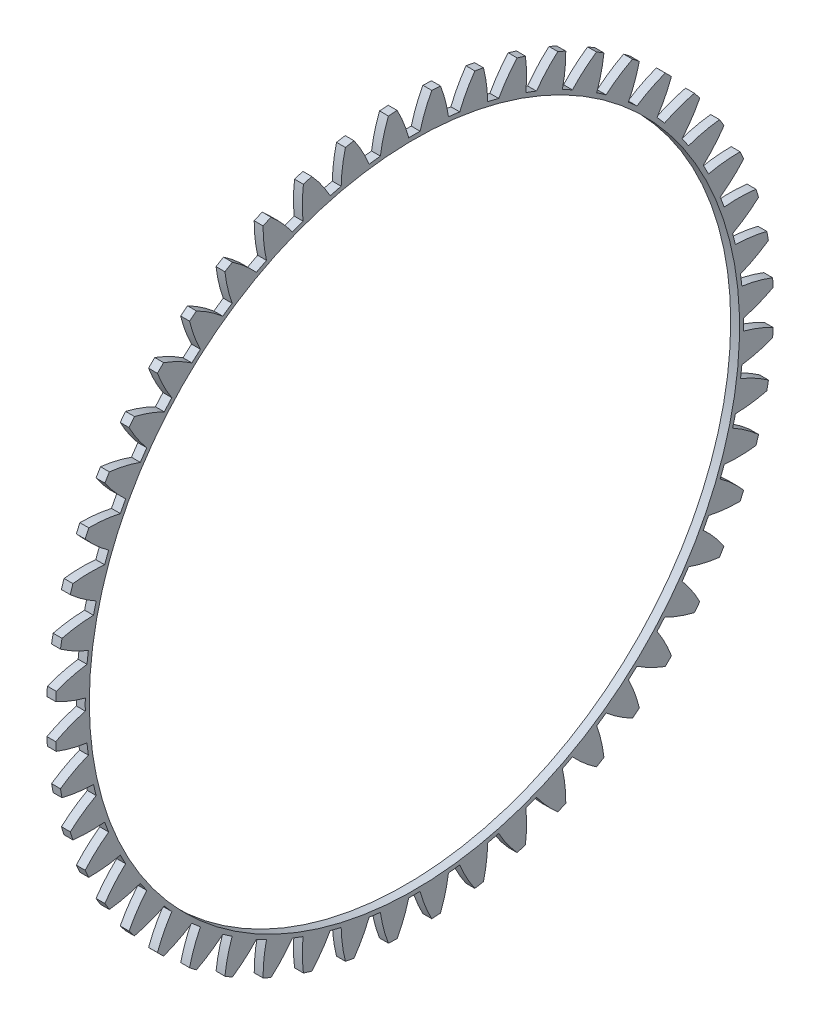
SolidWorks part; units mm, degrees
ref_plane "Plane1" through (0, 0, 0) normal (0, 0, 1) x (1, 0, 0)
ref_plane "Plane2" through (0, 0, 0) normal (0, 1, 0) x (1, 0, 0)
ref_plane "Plane3" through (0, 0, 0) normal (1, 0, 0) x (0, 0, -1)
sketch "HoldingSke" plane through (0, 0, 0) normal (0, 1, 0) x (1, 0, 0)
  line L0 (0, 0) -> (0.1368, -0.1751)
  line L1 (-15, 0) -> (100, 0) construction
  line L2 (0, 0) -> (-2.1039, 2.3779)
  line L3 (0, 0) -> (-11.863, 4.5341)
  line L4 (0, 0) -> (5.3169, 6.8053)
  line L5 (0, 0) -> (-46.8476, -17.4728)
  line L6 (0, 0) -> (-2.4869, -1.6779)
  line L7 (-2.1039, 2.3779) -> (8.6586, 51.2059)
  line L8 (-76.2, 54.61) -> (-64.8, 54.61)
  line L9 (-71.009, 38.7566) -> (-53.1078, 45.2721)
  line L10 (-76.2, 71.12) -> (104.1128, 71.12)
  line L11 (0, 0) -> (-3, 0)
  line L12 (-76.2, 101.6) -> (-76.053, 101.6)
  line L13 (24.9733, 27.94) -> (52.9518, 28.4284)
  line L14 (24.9733, 27.94) -> (24.9743, 27.94)
  line L15 (24.9733, 27.94) -> (100.4006, 29.5858)
  line L16 (-63.627, -4.5) -> (-12.827, -4.5)
  circle A0 centre (0, 0) radius 110
  circle A1 centre (0, 0) radius 37.5
  circle A2 centre (0, 0) radius 37.5
  circle A3 centre (0, 0) radius 110
  dimension "MHD" = 75
  dimension "Hub_dia" = 75
  dimension "Bore" = 220
  dimension "MBD" = 220
  dimension "Num_teeth" = 52
  dimension "Pitch" = 0.2222
  dimension "Overall_len" = 50
  dimension "Show_teeth" = 52
  dimension "Thickness" = 3
  dimension "OAL" = 50.0001
  dimension "T_dim" = 11.4
  dimension "Ap" = 20
  dimension "H" = 19.05
  dimension "Pitch_radius" = 180.3128
  dimension "Width" = 3
  dimension "Backlash" = 0.147
  dimension "Addendum_fac" = 1
  dimension "Dedendum_fac" = 1.25
  dimension "Clearance_fac" = 0.25
  dimension "Dedendum_add" = 0.001
  dimension "Module" = 4.5
sketch "BasProSke" plane through (0, 0, 0) normal (0, 1, 0) x (1, 0, 0)
  line L0 (-10, 0) -> (60, 0) construction
  line L1 (0, 0) -> (0, 121.5)
  line L2 (0, 0) -> (3, 0)
  line L3 (3, 0) -> (3, 121.5)
  line L4 (3, 121.5) -> (0, 121.5)
  dimension "Thickness" = 3
  dimension "Diameter" = 243
revolve "Base-Revolve" add sketch "BasProSke" angle 360 about L0
sketch "TooCutSke" plane through (0, 0, 0) normal (1, 0, 0) x (0, 0, -1)
  line L1 (0, 0) -> (0, 107) construction
  line L2 (0, 0) -> (-3.791, 116.9386) construction
  line L3 (0, 0) -> (-14.123, 233.4815) construction
  line L4 (-3.791, 116.9386) -> (-7.0615, 116.7407) construction
  arc A0 (1.9227, 111.3574) -> (-1.9227, 111.3574) centre (0, 0) ccw
  arc A1 (5.8749, 121.3833) -> (-5.8749, 121.3833) centre (0, 0) ccw
  circle A2 centre (0, 0) radius 117 construction
  circle A3 centre (0, 0) radius 109.944 construction
  arc A4 (-1.9227, 111.3574) -> (-5.8749, 121.3833) centre (-47.1485, 99.3213) ccw
  arc A5 (5.8749, 121.3833) -> (1.9227, 111.3574) centre (47.1485, 99.3213) ccw
  dimension "Root_dia" = 222.748
  dimension "Overcut_dia" = 243.0508
  dimension "Pitch_dia" = 234
  dimension "Base_dia" = 219.8881
  dimension "Flank_rad" = 46.8
  dimension "Half_ang" = 3.462
  dimension "Half_CT" = 3.2765
extrude "ToothCut" cut sketch "TooCutSke" along normal through all
fillet "Breaks" [suppressed] radius 0.09
fillet "RootFillets" [suppressed] radius 1.126
pattern_circular "TeethCuts" count 52 every 6.923 about axis through (-10, 0, 0) along (1, 0, 0) of "ToothCut", "RootFillets", "Breaks"
sketch "HubNeaOneSke" plane through (0, 0, 0) normal (-1, 0, 0) x (0, 0, 1)
  circle A0 centre (0, 0) radius 37.5
  dimension "Diameter" = 75
extrude "HubNearOne" [suppressed] add sketch "HubNeaOneSke" along normal blind 47.0001
sketch "HubNeaBotSke" plane through (0, 0, 0) normal (-1, 0, 0) x (0, 0, 1)
  circle A0 centre (0, 0) radius 37.5
  dimension "Diameter" = 75
extrude "HubNearBoth" [suppressed] add sketch "HubNeaBotSke" along normal blind 23.5
ref_plane "FarPln" through (3, 0, 0) normal (1, 0, 0) x (0, 0, -1)
sketch "HubFarSke" plane through (3, 0, 0) normal (1, 0, 0) x (0, 0, -1)
  circle A0 centre (0, 0) radius 37.5
  dimension "Diameter" = 75
extrude "HubFar" [suppressed] add sketch "HubFarSke" along normal blind 23.5
sketch "BorSke" plane through (0, 0, 0) normal (1, 0, 0) x (0, 0, -1)
  circle A0 centre (0, 0) radius 110
  dimension "Diameter" = 220
extrude "Bore" cut sketch "BorSke" along normal mid plane 100.0001
sketch "KeySke" plane through (0, 0, 0) normal (1, 0, 0) x (0, 0, -1)
  line L0 (-25, 0) -> (-25, 121.4)
  line L1 (-25, 121.4) -> (25, 121.4)
  line L2 (25, 121.4) -> (25, 0)
  line L3 (0, 0) -> (0, 34) construction
  line L4 (-25, 0) -> (25, 0)
  dimension "Offset" = 121.4
  dimension "Width" = 50
extrude "Keyway" [suppressed] cut sketch "KeySke" along normal mid plane 100.0001
pattern_circular "Keyway2" [suppressed] count 2 every 90 about axis through (-10, 0, 0) along (1, 0, 0)
equation "' \"Module@HoldingSke\" = 6.35"
equation "' \"Num_teeth@HoldingSke\" = 12"
equation "' \"Ap@HoldingSke\" =  20"
equation "' \"Ap@HoldingSke\" = 20"
equation "' \"Width@HoldingSke\" = 0.5 * 25.4"
equation "' \"Hub_dia@HoldingSke\"= 1 * 25.4"
equation "' \"Hub_dia@HoldingSke\" = 1 * 25.4"
equation "' \"Overall_len@HoldingSke\" = 1.0 * 25.4"
equation "' \"Bore@HoldingSke\" = 0.75 * 25.4"
equation "' \"T_dim@HoldingSke\" = 0.1 * 25.4"
equation "' \"Width@KeySke\" = 0.25 * 25.4"
equation "' \"Show_teeth@HoldingSke\" = 13"
equation "' \"Backlash@HoldingSke\" = 0.009 * 25.4"
equation "' \"Addendum_fac@HoldingSke\" = 1.0"
equation "' \"Dedendum_fac@HoldingSke\" = 1.25"
equation "' \"Dedendum_add@HoldingSke\" = 0.00005 * 25.4"
equation "' \"Clearance_fac@HoldingSke\" = 0.25"
equation "\"Pitch@HoldingSke\" = 1 / \"Module@HoldingSke\""
equation "\"Overcut_dia@TooCutSke\" = (\"Num_teeth@HoldingSke\" + 2 * \"Addendum_fac@HoldingSke\") / \"Pitch@HoldingSke\" + 0.002 * 25.4"
equation "\"Pitch_dia@TooCutSke\" = \"Num_teeth@HoldingSke\" / \"Pitch@HoldingSke\""
equation "\"Base_dia@TooCutSke\" = \"Num_teeth@HoldingSke\" / \"Pitch@HoldingSke\" * cos((\"Ap@HoldingSke\"  * 3.14159265 / 180))"
equation "\"Root_dia@TooCutSke\" = (\"Num_teeth@HoldingSke\" + 2) / \"Pitch@HoldingSke\" - 2 * (\"Addendum_fac@HoldingSke\" + \"Dedendum_fac@HoldingSke\") / \"Pitch@HoldingSke\" - \"Dedendum_add@HoldingSke\" * 2"
equation "\"Half_ang@TooCutSke\" = 180 / \"Num_teeth@HoldingSke\""
equation "\"Half_CT@TooCutSke\" = \"Num_teeth@HoldingSke\" / \"Pitch@HoldingSke\" * sin((3.14159265 / 2 / \"Num_teeth@HoldingSke\")) / 2 - 7 * \"Backlash@HoldingSke\" / 4"
equation "\"Flank_rad@TooCutSke\" = \"Num_teeth@HoldingSke\" / \"Pitch@HoldingSke\" / 5"
equation "\"Radius@RootFillets\" = \"Clearance_fac@HoldingSke\" / \"Pitch@HoldingSke\" + \"Dedendum_add@HoldingSke\""
equation "\"Break_rad@Breaks\" = 0.02 / \"Pitch@HoldingSke\""
equation "\"Thickness@HoldingSke\" = \"Width@HoldingSke\""
equation "\"OAL@HoldingSke\" = \"Thickness@HoldingSke\""
equation "\"MHD@HoldingSke\" = (\"Num_teeth@HoldingSke\" + 2) / \"Pitch@HoldingSke\" - 2 * (\"Addendum_fac@HoldingSke\" + \"Dedendum_fac@HoldingSke\")  / \"Pitch@HoldingSke\" - \"Dedendum_add@HoldingSke\" * 2"
equation "\"MBD@HoldingSke\" = (\"Num_teeth@HoldingSke\" + 2) / \"Pitch@HoldingSke\" - 2 * (\"Addendum_fac@HoldingSke\" + \"Dedendum_fac@HoldingSke\")  / \"Pitch@HoldingSke\" - \"Dedendum_add@HoldingSke\" * 2 - 0.002 * 25.4"
equation "\"MHD@HoldingSke\" = ((sgn( \"MHD@HoldingSke\" - \"Hub_dia@HoldingSke\" )-1)*( \"MHD@HoldingSke\" - \"Hub_dia@HoldingSke\" ))/-2+ \"Hub_dia@HoldingSke\""
equation "\"MBD@HoldingSke\" = ((sgn( \"MBD@HoldingSke\" - \"Bore@HoldingSke\" )-1)*( \"MBD@HoldingSke\" - \"Bore@HoldingSke\" ))/-2+ \"Bore@HoldingSke\""
equation "\"OAL@HoldingSke\" = ((sgn( \"OAL@HoldingSke\" - \"Overall_len@HoldingSke\" )+1)*( \"OAL@HoldingSke\" - \"Overall_len@HoldingSke\" ))/2 + \"Overall_len@HoldingSke\" + 0.000002 * 25.4"
equation "\"Num_teeth@TeethCuts\" = int( \"Show_teeth@HoldingSke\" ) + 1"
equation "\"Num_teeth@TeethCuts\" = ((sgn( \"Num_teeth@TeethCuts\" - \"Num_teeth@HoldingSke\" )-1)*( \"Num_teeth@TeethCuts\" - \"Num_teeth@HoldingSke\" ))/-2+ \"Num_teeth@HoldingSke\""
equation "\"Num_teeth@TeethCuts\" = ((sgn( \"Num_teeth@TeethCuts\" - 2.0)+1)*( \"Num_teeth@TeethCuts\" - 2.0))/2 +2.0"
equation "\"Angle@TeethCuts\" = 360.0 / \"Num_teeth@HoldingSke\""
equation "\"Diameter@BasProSke\" = (\"Num_teeth@HoldingSke\" + 2 * \"Addendum_fac@HoldingSke\") / \"Pitch@HoldingSke\""
equation "\"Thickness@BasProSke\"  = \"Thickness@HoldingSke\""
equation "' \"Fillet_rad@BasProSke\" =  \"Thickness@HoldingSke\" * 0.05"
equation "' \"Fillet_rad@BasProSke\" = \"Thickness@HoldingSke\" * 0.05"
equation "\"MHD@HoldingSke\" = ((sgn( \"MHD@HoldingSke\" - \"Root_dia@TooCutSke\" )-1)*( \"MHD@HoldingSke\" - \"Root_dia@TooCutSke\" ))/-2+ \"Root_dia@TooCutSke\""
equation "\"Diameter@HubNeaOneSke\" = \"MHD@HoldingSke\""
equation "\"Length@HubNearOne\" = \"OAL@HoldingSke\" - \"Thickness@BasProSke\""
equation "\"Diameter@HubNeaBotSke\" = \"MHD@HoldingSke\""
equation "\"Length@HubNearBoth\" = ( \"OAL@HoldingSke\" - \"Thickness@BasProSke\" ) / 2.0"
equation "\"Thickness@FarPln\" = \"Thickness@BasProSke\""
equation "\"Diameter@HubFarSke\" = \"MHD@HoldingSke\""
equation "\"Length@HubFar\" = ( \"OAL@HoldingSke\" - \"Thickness@BasProSke\" ) / 2.0"
equation "\"Diameter@BorSke\" = \"MBD@HoldingSke\""
equation "\"D1@Bore\" = \"OAL@HoldingSke\" * 2.0"
equation "\"D1@Keyway\" = \"OAL@HoldingSke\" * 2.0"
equation "\"Offset@KeySke\" = \"T_dim@HoldingSke\" + \"MBD@HoldingSke\" / 2.0"
